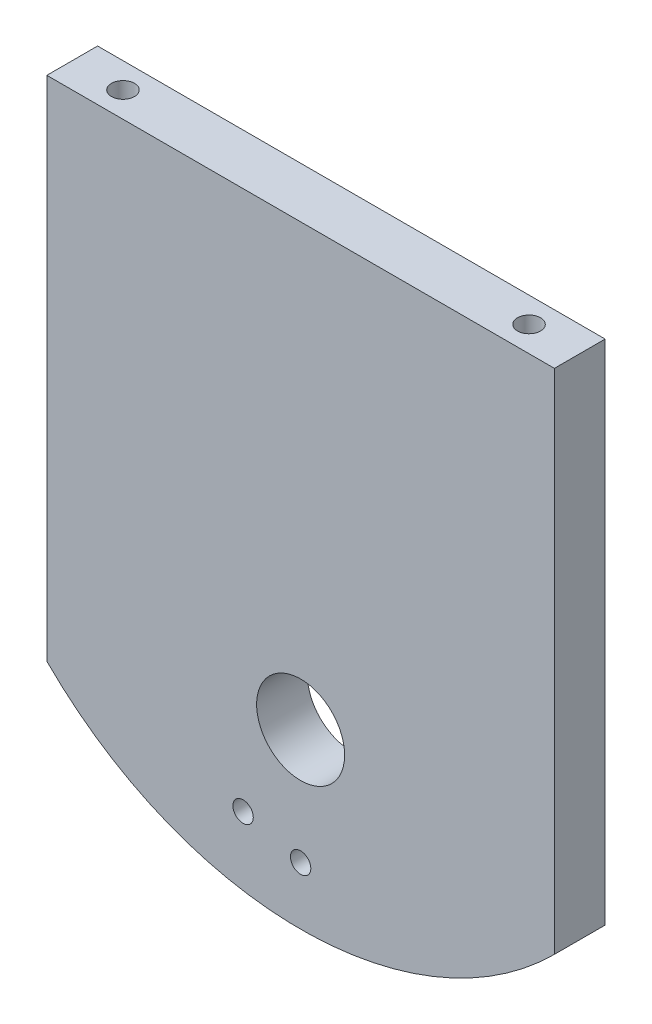
SolidWorks part; units mm, degrees
ref_plane "Front Plane" through (0, 0, 0) normal (0, 0, 1) x (1, 0, 0)
ref_plane "Top Plane" through (0, 0, 0) normal (0, 1, 0) x (1, 0, 0)
ref_plane "Right Plane" through (0, 0, 0) normal (1, 0, 0) x (0, 0, -1)
sketch "Sketch2" plane through (0, 0, 0) normal (0, 0, 1) x (1, 0, 0)
  line L1 (-75, -45) -> (75, -45)
  line L2 (-75, -45) -> (-75, 45)
  line L3 (-75, 45) -> (75, 45)
  line L4 (75, -45) -> (75, 45)
  line L5 (-75, -45) -> (75, 45) construction
  line L6 (-75, 45) -> (75, -45) construction
  line L7 (-75, -45) -> (75, -45)
  line L8 (-75, -45) -> (-75, -105)
  line L9 (-75, -105) -> (75, -105)
  line L10 (75, -45) -> (75, -105)
  arc A0 (-75, -105) -> (75, -105) centre (0, -30) ccw
  point P0 (0, 0)
  dimension "D1" = 150
  dimension "D2" = 90
  dimension "D3" = 60
extrude "Boss-Extrude1" add sketch "Sketch2" along normal blind 15 contours L1 L4 L3 L2 | L10 L1 L8 L9 | L9 A0
sketch "Sketch3" plane through (0, 0, 15) normal (0, 0, 1) x (1, 0, 0)
  line L0 (0, 45) -> (0, -136.066) construction
  line L1 (-75, 45) -> (75, 45) construction
  line L2 (-17, -114.4449) -> (0, -85) construction
  arc A0 (-75, -105) -> (75, -105) centre (0, -30) ccw construction
  circle A1 centre (0, -85) radius 13.005
  circle A2 centre (0, -85) radius 34
  circle A3 centre (-17, -114.4449) radius 3.01
  circle A4 centre (0, -119) radius 3.01
  point P10 (0, -119)
  point P11 (-17, -114.4449)
  dimension "D1" = 130
  dimension "D2" = 30
extrude "Cut-Extrude1" cut sketch "Sketch3" against normal through all contours A1 | A2 A4 | A2 A4 | A2 A3 | A2 A3
sketch "Sketch6" plane through (0, 0, 0) normal (0, 0, -1) x (-1, 0, 0)
  line L3 (-75, -105) -> (-75, 45) construction
  line L4 (75, -105) -> (75, 45) construction
  line L5 (75, 45) -> (-75, 45) construction
  line L6 (0, 45) -> (0, -136.066) construction
  line L7 (-75, -50) -> (75, -50) construction
  arc A0 (-75, -105) -> (75, -105) centre (0, -30) ccw construction
  point P0 (-37.5, -50)
  point P1 (37.5, -50)
  dimension "D1" = 37.5
  dimension "D2" = 95
  dimension "D3" = 37.5
hole_wizard "Tap Drill for M8x1.25 Tap1" positions "Sketch8" profile "Sketch7" hole size "M8x1.25" standard "ANSI Metric"
sketch "Sketch8" plane through (0, 0, 0) normal (0, 0, -1) x (-1, 0, 0)
  point P0 (-37.5, -50)
  point P3 (37.5, -50)
sketch "Sketch7" plane through (37.5, -50, 0) normal (1, 0, 0) x (0, 1, 0)
  line L0 (0, 0) -> (0, 12.0429)
  line L1 (0, 12.0429) -> (3.4, 10)
  line L2 (3.4, 10) -> (3.4, 0)
  line L5 (3.4, 0) -> (0, 0)
  line L10 (0, 12.0429) -> (-3.4, 10) construction
  line L11 (0, -6.35) -> (0, 107.95) construction
  dimension "Hole Dia." = 6.8
  dimension "Hole Depth" = 10
  dimension "Drill Angle" = 118
sketch "Sketch9" plane through (0, 45, 0) normal (0, 1, 0) x (1, 0, 0)
  line L0 (-75, -7.5) -> (75, -7.5) construction
  line L1 (-75, -15) -> (-75, 0) construction
  line L2 (75, -15) -> (75, 0) construction
  line L3 (0, 0) -> (0, -15) construction
  line L4 (75, 0) -> (-75, 0) construction
  line L5 (-75, -15) -> (75, -15) construction
  point P12 (-60, -7.5)
  point P13 (60, -7.5)
  dimension "D1" = 60
  dimension "D2" = 60
hole_wizard "Tap Drill for M8x1.25 Tap2" positions "Sketch12" profile "Sketch10" hole size "M8x1.25" standard "ANSI Metric"
sketch "Sketch12" plane through (0, 45, 0) normal (0, 1, 0) x (1, 0, 0)
  point P0 (-60, -7.5)
  point P3 (60, -7.5)
sketch "Sketch10" plane through (-60, 45, 7.5) normal (1, 0, 0) x (0, 0, 1)
  line L0 (0, 0) -> (0, 42.0429)
  line L1 (0, 42.0429) -> (3.4, 40)
  line L2 (3.4, 40) -> (3.4, 0)
  line L5 (3.4, 0) -> (0, 0)
  line L10 (0, 42.0429) -> (-3.4, 40) construction
  line L11 (0, -6.35) -> (0, 107.95) construction
  dimension "Hole Dia." = 6.8
  dimension "Hole Depth" = 40
  dimension "Drill Angle" = 118
